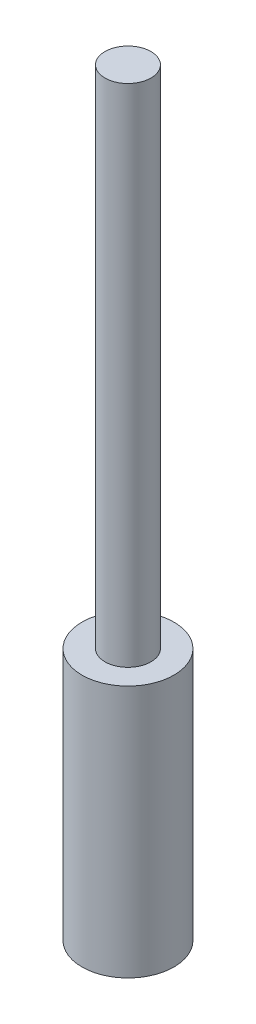
SolidWorks part; units mm, degrees
ref_plane "Front Plane" through (0, 0, 0) normal (0, 0, 1) x (1, 0, 0)
ref_plane "Top Plane" through (0, 0, 0) normal (0, 1, 0) x (1, 0, 0)
ref_plane "Right Plane" through (0, 0, 0) normal (1, 0, 0) x (0, 0, -1)
sketch "Sketch1" plane through (0, 0, 0) normal (0, 1, 0) x (1, 0, 0)
  circle A0 centre (0, 0) radius 10
  dimension "D1" = 20
extrude "Boss-Extrude1" add sketch "Sketch1" along normal blind 55
sketch "Sketch2" plane through (0, 55, 0) normal (0, 1, 0) x (1, 0, 0)
  circle A0 centre (0, 0) radius 5
  dimension "D1" = 10
extrude "Boss-Extrude2" add sketch "Sketch2" along normal blind 110
